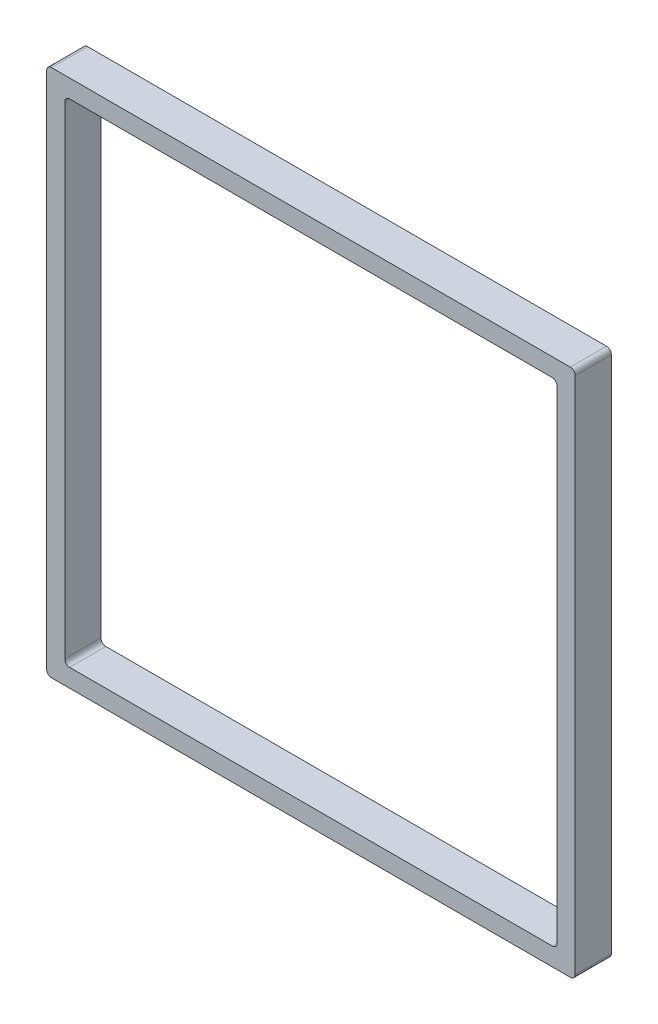
SolidWorks part; units mm, degrees
material "Copper"
ref_plane "Front Plane" through (0, 0, 0) normal (0, 0, 1) x (1, 0, 0)
ref_plane "Top Plane" through (0, 0, 0) normal (0, 1, 0) x (1, 0, 0)
ref_plane "Right Plane" through (0, 0, 0) normal (1, 0, 0) x (0, 0, -1)
sketch "Sketch1" plane through (0, 0, 0) normal (0, 0, 1) x (1, 0, 0)
  line L1 (-129.54, -129.54) -> (129.54, -129.54)
  line L2 (-129.54, -129.54) -> (-129.54, 129.54)
  line L3 (-129.54, 129.54) -> (129.54, 129.54)
  line L4 (129.54, -129.54) -> (129.54, 129.54)
  line L5 (-129.54, -129.54) -> (129.54, 129.54) construction
  line L6 (-129.54, 129.54) -> (129.54, -129.54) construction
  line L7 (-139.065, -139.065) -> (139.065, -139.065)
  line L8 (-139.065, -139.065) -> (-139.065, 139.065)
  line L9 (-139.065, 139.065) -> (139.065, 139.065)
  line L10 (139.065, -139.065) -> (139.065, 139.065)
  line L11 (-139.065, -139.065) -> (139.065, 139.065) construction
  line L12 (-139.065, 139.065) -> (139.065, -139.065) construction
  point P0 (0, 0)
  point P6 (0, 0)
  dimension "D1" = 259.08
  dimension "D2" = 259.08
  dimension "D3" = 278.13
  dimension "D4" = 278.13
extrude "Boss-Extrude1" add sketch "Sketch1" along normal blind 19.05
fillet "Fillet1" radius 2.54 8 edges at (129.54, 129.54, 9.525) (129.54, -129.54, 9.525) (-129.54, -129.54, 9.525) (-129.54, 129.54, 9.525) (139.065, -139.065, 9.525) (-139.065, -139.065, 9.525) (-139.065, 139.065, 9.525) (139.065, 139.065, 9.525)
sketch "Sketch2" plane through (0, 0, 0) normal (0, 0, -1) x (-1, 0, 0)
  circle A0 centre (0, 0) radius 127
